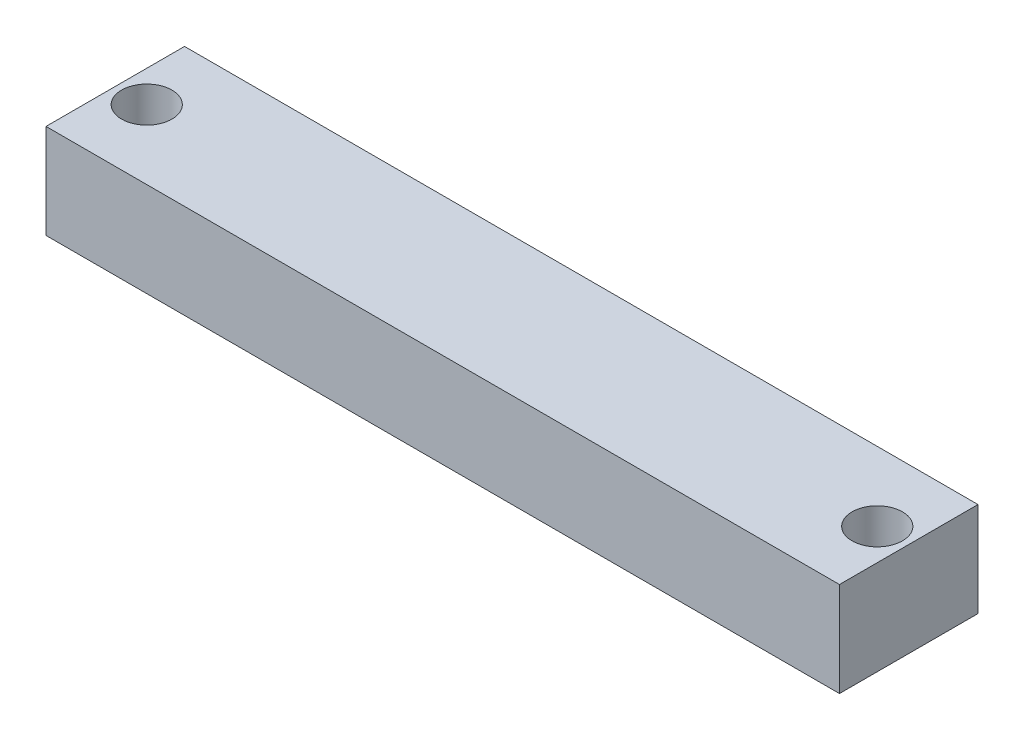
SolidWorks part; units mm, degrees
ref_plane "Front Plane" through (0, 0, 0) normal (0, 0, 1) x (1, 0, 0)
ref_plane "Top Plane" through (0, 0, 0) normal (0, 1, 0) x (1, 0, 0)
ref_plane "Right Plane" through (0, 0, 0) normal (1, 0, 0) x (0, 0, -1)
sketch "Sketch5" plane through (0, 0, 0) normal (0, 1, 0) x (1, 0, 0)
  line L1 (0, 0) -> (126, 0)
  line L2 (0, 0) -> (0, 22)
  line L3 (0, 22) -> (126, 22)
  line L4 (126, 0) -> (126, 22)
  dimension "D1" = 22
  dimension "D2" = 126
extrude "Boss-Extrude5" add sketch "Sketch5" along normal blind 15
sketch "Sketch6" plane through (0, 0, 0) normal (-1, 0, 0) x (0, 0, 1)
  circle A0 centre (-11.222, 2.7815) radius 1.2009
extrude "Cut-Extrude1" cut sketch "Sketch6" against normal blind 10
sketch "Sketch7" plane through (0, 15, 0) normal (0, 1, 0) x (1, 0, 0)
  line L0 (0, 22) -> (0, 0) construction
  line L1 (126, 22) -> (0, 22) construction
  line L2 (63, 22) -> (63, 0) construction
  line L3 (0, 0) -> (126, 0) construction
  circle A0 centre (5, 11) radius 4
  circle A1 centre (121, 11) radius 4
  dimension "D1" = 8
  dimension "D2" = 5
  dimension "D3" = 11
extrude "Cut-Extrude2" cut sketch "Sketch7" against normal through all
